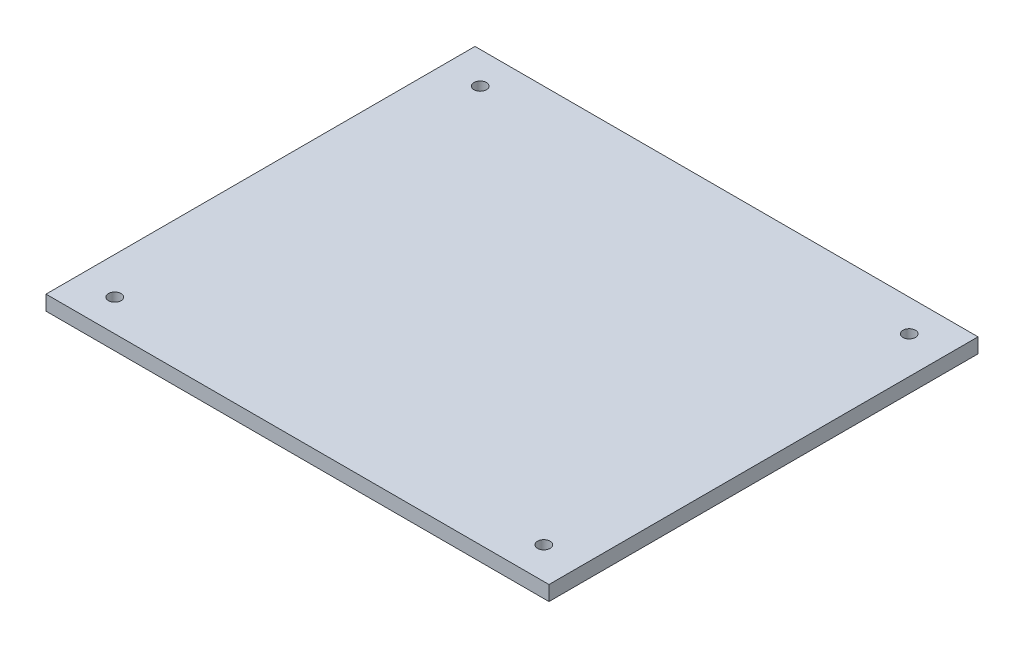
SolidWorks part; units mm, degrees
ref_plane "Front Plane" through (0, 0, 0) normal (0, 0, 1) x (1, 0, 0)
ref_plane "Top Plane" through (0, 0, 0) normal (0, 1, 0) x (1, 0, 0)
ref_plane "Right Plane" through (0, 0, 0) normal (1, 0, 0) x (0, 0, -1)
sketch "Sketch1" plane through (0, 0, 0) normal (0, 1, 0) x (1, 0, 0)
  line L1 (0, 0) -> (172.72, 0)
  line L2 (0, 0) -> (0, 147.32)
  line L3 (0, 147.32) -> (172.72, 147.32)
  line L4 (172.72, 0) -> (172.72, 147.32)
  dimension "D1" = 172.72
  dimension "D2" = 147.32
extrude "Boss-Extrude1" add sketch "Sketch1" along normal blind 5.08
sketch "Sketch3" plane through (0, 5.08, 0) normal (0, 1, 0) x (1, 0, 0)
  line L0 (0, 147.32) -> (0, 0) construction
  line L1 (172.72, 147.32) -> (0, 147.32) construction
  line L2 (172.72, 0) -> (172.72, 147.32) construction
  line L3 (0, 0) -> (172.72, 0) construction
  circle A0 centre (12.7, 136.398) radius 2.159
  circle A1 centre (160.02, 136.398) radius 2.159
  circle A2 centre (160.02, 10.922) radius 2.159
  circle A3 centre (12.7, 10.922) radius 2.159
  dimension "D1" = 4.318
  dimension "D2" = 12.7
  dimension "D3" = 10.922
  dimension "D4" = 12.7
  dimension "D5" = 10.922
  dimension "D6" = 12.7
  dimension "D7" = 10.922
  dimension "D8" = 12.7
  dimension "D9" = 10.922
extrude "Cut-Extrude1" cut sketch "Sketch3" against normal through all
